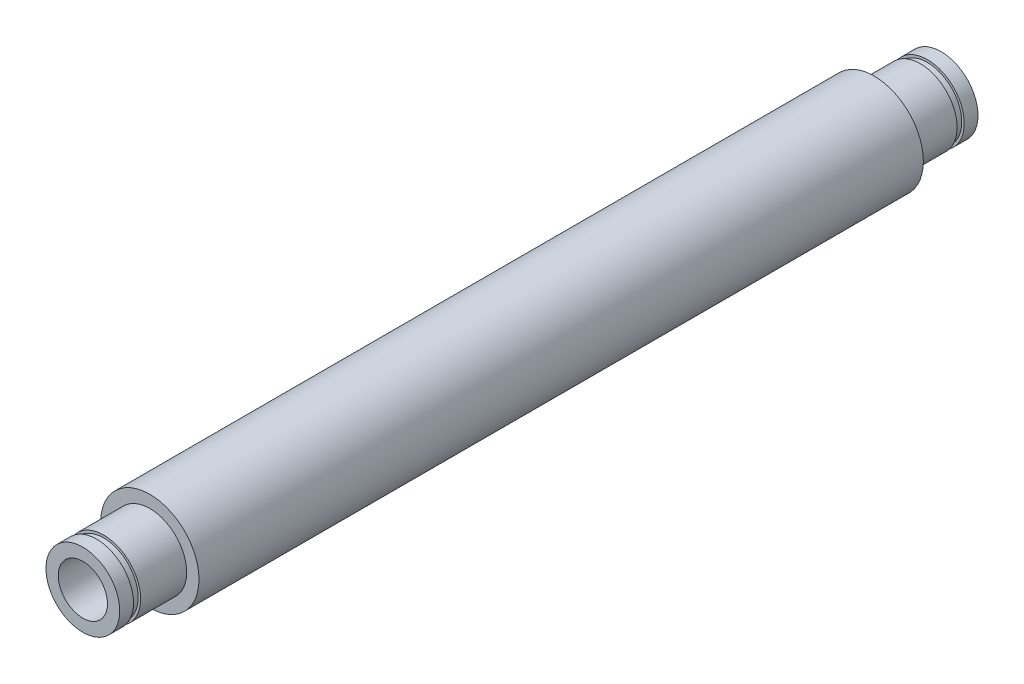
SolidWorks part; units mm, degrees
ref_plane "Front Plane" through (0, 0, 0) normal (0, 0, 1) x (1, 0, 0)
ref_plane "Top Plane" through (0, 0, 0) normal (0, 1, 0) x (1, 0, 0)
ref_plane "Right Plane" through (0, 0, 0) normal (1, 0, 0) x (0, 0, -1)
sketch "Sketch1" plane through (0, 0, 0) normal (0, 0, 1) x (1, 0, 0)
  circle A0 centre (0, 0) radius 3.175
  dimension "D1" = 6.35
extrude "Boss-Extrude1" add sketch "Sketch1" along normal mid plane 55.372
sketch "Sketch2" plane through (0, 0, 27.686) normal (0, 0, 1) x (1, 0, 0)
  circle A0 centre (0, 0) radius 2.3813
  circle A1 centre (0, 0) radius 3.175
  dimension "D1" = 4.7625
extrude "Cut-Extrude1" cut sketch "Sketch2" against normal blind 4.318
ref_plane "Plane1" through (0, 0, 26.797) normal (0, 0, 1) x (1, 0, 0)
sketch "Sketch3" plane through (0, 0, 26.797) normal (0, 0, 1) x (1, 0, 0)
  circle A0 centre (0, 0) radius 2.3813
  circle A1 centre (0, 0) radius 2.2225
  dimension "D1" = 4.445
extrude "Cut-Extrude2" cut sketch "Sketch3" against normal blind 0.4572
fillet "Fillet1" [suppressed] radius 0.508
sketch "Sketch4" plane through (0, 0, 27.686) normal (0, 0, 1) x (1, 0, 0)
  circle A0 centre (0, 0) radius 1.5875
  dimension "D1" = 3.175
extrude "Cut-Extrude3" cut sketch "Sketch4" against normal through all
mirror "Mirror1" about plane through (0, 0, 0) normal (0, 0, 1) of "Cut-Extrude2", "Cut-Extrude1", "Fillet1"
